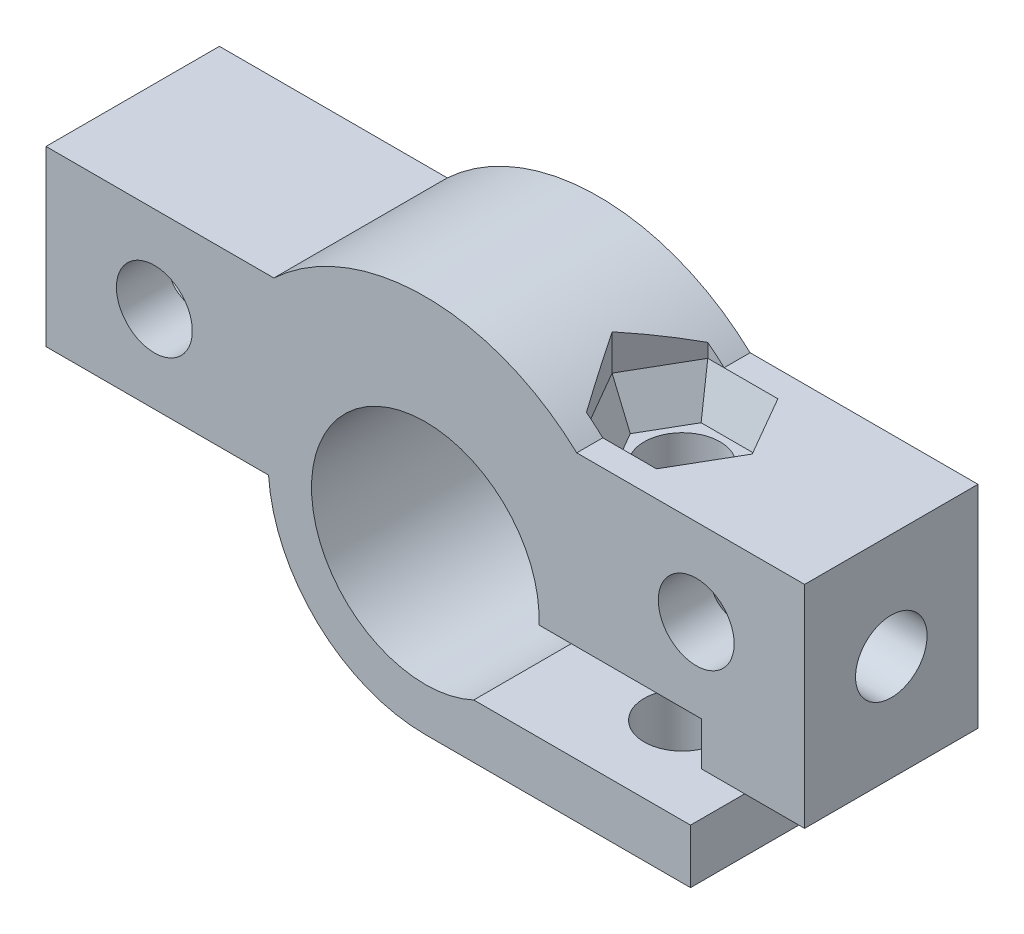
SolidWorks part; units mm, degrees
ref_plane "Plano frontal" through (0, 0, 0) normal (0, 0, 1) x (1, 0, 0)
ref_plane "Plano superior" through (0, 0, 0) normal (0, 1, 0) x (1, 0, 0)
ref_plane "Plano direito" through (0, 0, 0) normal (1, 0, 0) x (0, 0, -1)
sketch "Esboço1" plane through (0, 0, 0) normal (0, 0, 1) x (1, 0, 0)
  line L0 (17.5, 7.5) -> (6.9866, 7.5)
  line L1 (15.8072, -2.25) -> (12.7361, -2.25)
  line L2 (0, 0) -> (0, 8.1134) construction
  line L3 (-17.5, 7.5) -> (-6.9866, 7.5)
  line L4 (-17.5, -0.5) -> (-7.2327, -0.5)
  line L5 (0, -7.25) -> (12.2361, -7.25)
  line L6 (12.2361, -7.25) -> (12.2361, -4.75)
  line L7 (12.2361, -4.75) -> (2.2361, -4.75)
  line L8 (-17.5, 7.5) -> (-17.5, -0.5)
  line L15 (17.5, 7.5) -> (17.5, -2.25)
  line L16 (17.5, -2.25) -> (15.8072, -2.25)
  line L23 (5.244, -0.25) -> (12.7361, -0.25)
  line L24 (12.7361, -0.25) -> (12.7361, -2.25)
  arc A0 (6.9866, 7.5) -> (-6.9866, 7.5) centre (0, 0) ccw
  arc A1 (5.244, -0.25) -> (2.2361, -4.75) centre (0, 0) ccw
  circle A3 centre (12.5, 3.5) radius 1.75
  circle A4 centre (-12.5, 3.5) radius 1.75
  arc A6 (-7.2327, -0.5) -> (0, -7.25) centre (0, 0) ccw
  point P1 (-17.5, 3.5)
  point P3 (17.8193, 9.9747)
  point P7 (16.7306, 7.881)
  dimension "D2" = 10.5
  dimension "D3" = 5
  dimension "D4" = 4
  dimension "D5" = 3.5
  dimension "D7" = 2
  dimension "D1" = 25
  dimension "D6" = 2.5
  dimension "D8" = 3.5
  dimension "D9" = 2.5
  dimension "D10" = 5
  dimension "D14" = 10
  dimension "D15" = 0.5
  dimension "D16" = 2
extrude "Ressalto-extrusão1" add sketch "Esboço1" along normal blind 8
sketch "Esboço2" plane through (17.5, 0, 0) normal (1, 0, 0) x (0, 0, -1)
  line L0 (-8, 7.5) -> (0, -2.25) construction
  circle A0 centre (-4, 2.625) radius 1.65
  dimension "D1" = 3.3
extrude "Corte-extrusão1" cut sketch "Esboço2" against normal blind 7
mirror "Espelhar1" about plane through (0, 0, 0) normal (1, 0, 0) of "Corte-extrusão1"
sketch "Esboço3" plane through (0, -7.25, 0) normal (0, -1, 0) x (1, 0, 0)
  line L0 (5.5, 0) -> (5.5, 8) construction
  line L1 (0, 0) -> (12.2361, 0) construction
  line L2 (0, 8) -> (12.2361, 8) construction
  line L3 (0, 8) -> (0, 0) construction
  circle A0 centre (7.85, 4) radius 1.75
  point P8 (0, 4)
  point P11 (5.5, 4)
  point P12 (5.5, 8)
  point P13 (7.85, 11.5926)
  dimension "D2" = 0.6
  dimension "D3" = 3.5
  dimension "D1" = 5.5
  dimension "D4" = 4
extrude "Corte-extrusão2" cut sketch "Esboço3" against normal through all
sketch "Esboço4" plane through (0, 7.5, 0) normal (0, 1, 0) x (1, 0, 0)
  line L1 (11.0832, -4) -> (9.4666, -1.2)
  line L2 (9.4666, -1.2) -> (6.2334, -1.2)
  line L3 (6.2334, -1.2) -> (4.6168, -4)
  line L4 (4.6168, -4) -> (6.2334, -6.8)
  line L5 (6.2334, -6.8) -> (9.4666, -6.8)
  line L6 (9.4666, -6.8) -> (11.0832, -4)
  circle A0 centre (7.85, -4) radius 2.8 construction
  circle A1 centre (7.85, -4) radius 1.75 construction
  dimension "D1" = 5.6
extrude "Corte-extrusão3" cut sketch "Esboço4" against normal blind 2 draft 20 and the other way blind 6
